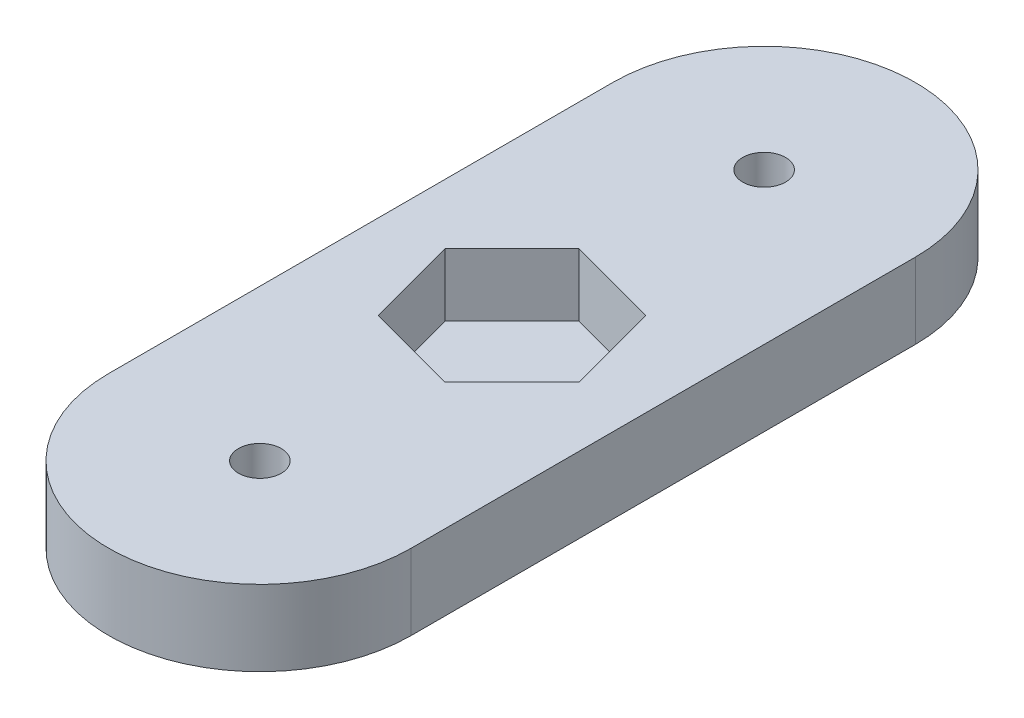
SolidWorks part; units mm, degrees
material "ABS PC"
ref_plane "Front Plane" through (0, 0, 0) normal (0, 0, 1) x (1, 0, 0)
ref_plane "Top Plane" through (0, 0, 0) normal (0, 1, 0) x (1, 0, 0)
ref_plane "Right Plane" through (0, 0, 0) normal (1, 0, 0) x (0, 0, -1)
sketch "Sketch1" plane through (0, 0, 0) normal (0, 1, 0) x (1, 0, 0)
  line L0 (0, 0) -> (0, 40) construction
  line L1 (-12, 0) -> (-12, 40)
  line L2 (12, 0) -> (12, 40)
  arc A0 (-12, 0) -> (12, 0) centre (0, 0) ccw
  arc A1 (12, 40) -> (-12, 40) centre (0, 40) ccw
  circle A2 centre (0, 40) radius 1.7
  circle A3 centre (0, 0) radius 1.7
  point P3 (0, 20)
  dimension "D2" = 40
  dimension "D3" = 3.4
  dimension "D1" = 24
extrude "Boss-Extrude1" add sketch "Sketch1" along normal blind 6
sketch "Sketch2" plane through (0, 6, 0) normal (0, 1, 0) x (1, 0, 0)
  line L0 (12, 0) -> (12, 40) construction
  line L1 (1.9426, 12.7502) -> (7.2498, 18.0574)
  line L2 (7.2498, 18.0574) -> (5.3072, 25.3072)
  line L3 (5.3072, 25.3072) -> (-1.9426, 27.2498)
  line L4 (-1.9426, 27.2498) -> (-7.2498, 21.9426)
  line L5 (-7.2498, 21.9426) -> (-5.3072, 14.6928)
  line L6 (-5.3072, 14.6928) -> (1.9426, 12.7502)
  line L7 (-12, 40) -> (-12, 0) construction
  circle A0 centre (0, 20) radius 6.5 construction
  dimension "D1" = 13
  dimension "D2" = 12
  dimension "D3" = 20
  dimension "D4" = 75
extrude "Cut-Extrude1" cut sketch "Sketch2" against normal blind 5
